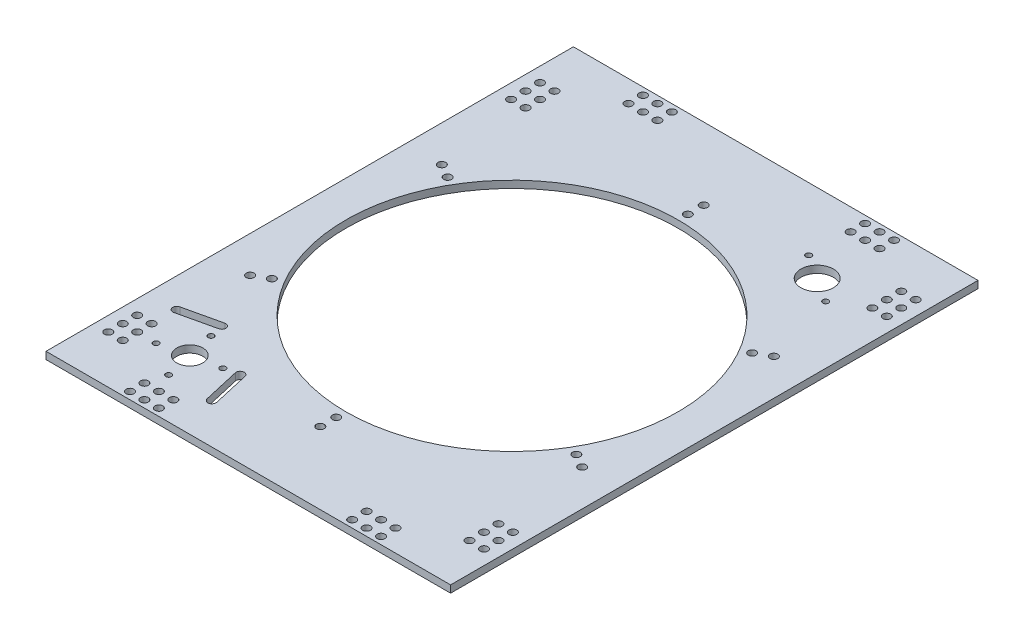
SolidWorks part; units mm, degrees
material "5052-H32"
ref_plane "Front Plane" through (0, 0, 0) normal (0, 0, 1) x (1, 0, 0)
ref_plane "Top Plane" through (0, 0, 0) normal (0, 1, 0) x (1, 0, 0)
ref_plane "Right Plane" through (0, 0, 0) normal (1, 0, 0) x (0, 0, -1)
sketch "Sketch1" plane through (0, 0, 0) normal (0, 1, 0) x (1, 0, 0)
  line L0 (-177.8, 231.775) -> (-177.8, -231.775)
  line L1 (-177.8, -231.775) -> (177.8, -231.775)
  line L2 (177.8, -231.775) -> (177.8, 231.775)
  line L3 (177.8, 231.775) -> (-177.8, 231.775)
  line L4 (0, 231.775) -> (0, -231.775) construction
  line L5 (-177.8, 0) -> (177.8, 0) construction
  line L6 (-127, 231.775) -> (-127, 206.375) construction
  line L7 (-127, 206.375) -> (-177.8, 206.375) construction
  line L8 (127, 206.375) -> (177.8, 206.375) construction
  line L9 (127, 231.775) -> (127, 206.375) construction
  line L10 (-127, -206.375) -> (-177.8, -206.375) construction
  line L11 (-127, -231.775) -> (-127, -206.375) construction
  line L12 (127, -231.775) -> (127, -206.375) construction
  line L13 (127, -206.375) -> (177.8, -206.375) construction
  line L14 (-127, -231.775) -> (-127, -203.2) construction
  line L15 (-127, -203.2) -> (-73.025, -203.2) construction
  line L16 (-73.025, -203.2) -> (-73.025, -231.775) construction
  line L17 (-177.8, -152.4) -> (-142.875, -152.4) construction
  line L18 (-142.875, -152.4) -> (-142.875, -206.375) construction
  line L19 (-116.9693, -147.6117) -> (-87.1462, -166.9791) construction
  line L29 (-102.1471, -157.2927) -> (0, 0) construction
  line L30 (-116.9693, -147.6117) -> (-105.9042, -195.8638) construction
  line L31 (-74.7675, -164.1404) -> (-67.387, -196.325) construction
  line L32 (-71.3015, -163.3456) -> (-63.9209, -195.5302)
  line L33 (-78.2336, -164.9352) -> (-70.853, -197.1198)
  line L34 (-87.1462, -166.9791) -> (-74.7675, -164.1404) construction
  line L35 (-118.3656, -141.4602) -> (-81.0867, -165.6694) construction
  line L36 (-81.0867, -165.6694) -> (-105.2959, -202.9483) construction
  line L37 (-105.2959, -202.9483) -> (-142.5748, -178.7391) construction
  line L38 (-142.5748, -178.7391) -> (-118.3656, -141.4602) construction
  line L39 (-116.9693, -147.6117) -> (-119.808, -135.233) construction
  line L40 (-119.808, -135.233) -> (-151.9926, -142.6136) construction
  line L41 (-102.1471, -157.2927) -> (-111.4368, -171.7378) construction
  line L42 (-119.0132, -138.6991) -> (-151.1978, -146.0796)
  line L43 (-120.6028, -131.767) -> (-152.7874, -139.1475)
  line L44 (0, 0) -> (105.6055, 162.6182) construction
  line L45 (84.3033, 176.4521) -> (126.9077, 148.7844) construction
  circle A0 centre (0, 0) radius 168.5 construction
  circle A1 centre (0, 0) radius 146.05
  circle A2 centre (0, 168.5) radius 3.429
  circle A3 centre (145.9253, 84.25) radius 3.429
  circle A4 centre (145.9253, -84.25) radius 3.429
  circle A5 centre (0, -168.5) radius 3.429
  circle A6 centre (-145.9253, -84.25) radius 3.429
  circle A7 centre (-145.9253, 84.25) radius 3.429
  circle A8 centre (-165.1, 189.7126) radius 3.429
  circle A9 centre (-152.4, 189.7126) radius 3.429
  circle A10 centre (-152.4, 177.0126) radius 3.429
  circle A11 centre (-165.1, 177.0126) radius 3.429
  circle A12 centre (-152.4, 164.3126) radius 3.429
  circle A13 centre (-165.1, 164.3126) radius 3.429
  circle A14 centre (165.1, 164.3126) radius 3.429
  circle A15 centre (152.4, 164.3126) radius 3.429
  circle A16 centre (165.1, 177.0126) radius 3.429
  circle A17 centre (152.4, 177.0126) radius 3.429
  circle A18 centre (152.4, 189.7126) radius 3.429
  circle A19 centre (165.1, 189.7126) radius 3.429
  circle A20 centre (165.1, -189.7126) radius 3.429
  circle A21 centre (152.4, -189.7126) radius 3.429
  circle A22 centre (152.4, -177.0126) radius 3.429
  circle A23 centre (165.1, -177.0126) radius 3.429
  circle A24 centre (152.4, -164.3126) radius 3.429
  circle A25 centre (165.1, -164.3126) radius 3.429
  circle A26 centre (-165.1, -164.3126) radius 3.429
  circle A27 centre (-152.4, -164.3126) radius 3.429
  circle A28 centre (-165.1, -177.0126) radius 3.429
  circle A29 centre (-152.4, -177.0126) radius 3.429
  circle A30 centre (-152.4, -189.7126) radius 3.429
  circle A31 centre (-165.1, -189.7126) radius 3.429
  circle A32 centre (-110.3376, 225.425) radius 3.429
  circle A33 centre (-97.6376, 225.425) radius 3.429
  circle A34 centre (-84.9376, 225.425) radius 3.429
  circle A35 centre (-97.6376, 212.725) radius 3.429
  circle A36 centre (-84.9376, 212.725) radius 3.429
  circle A37 centre (-110.3376, 212.725) radius 3.429
  circle A38 centre (110.3376, 212.725) radius 3.429
  circle A39 centre (84.9376, 212.725) radius 3.429
  circle A40 centre (97.6376, 212.725) radius 3.429
  circle A41 centre (84.9376, 225.425) radius 3.429
  circle A42 centre (97.6376, 225.425) radius 3.429
  circle A43 centre (110.3376, 225.425) radius 3.429
  circle A44 centre (110.3376, -225.425) radius 3.429
  circle A45 centre (97.6376, -225.425) radius 3.429
  circle A46 centre (84.9376, -225.425) radius 3.429
  circle A47 centre (97.6376, -212.725) radius 3.429
  circle A48 centre (84.9376, -212.725) radius 3.429
  circle A49 centre (110.3376, -212.725) radius 3.429
  circle A50 centre (-110.3376, -212.725) radius 3.429
  circle A51 centre (-84.9376, -212.725) radius 3.429
  circle A52 centre (-97.6376, -212.725) radius 3.429
  circle A53 centre (-84.9376, -225.425) radius 3.429
  circle A54 centre (-97.6376, -225.425) radius 3.429
  circle A55 centre (-110.3376, -225.425) radius 3.429
  arc A63 (-119.0132, -138.6991) -> (-120.6028, -131.767) centre (-119.808, -135.233) ccw
  arc A64 (-152.7874, -139.1475) -> (-151.1978, -146.0796) centre (-151.9926, -142.6136) ccw
  circle A69 centre (-116.9693, -147.6117) radius 2.54
  circle A70 centre (-87.1462, -166.9791) radius 2.54
  circle A71 centre (-105.9042, -195.8638) radius 2.54
  circle A72 centre (-135.5628, -177.2704) radius 2.54
  circle A73 centre (-111.4368, -171.7378) radius 11.43
  circle A74 centre (-111.4368, -171.7378) radius 21.0058 construction
  arc A75 (-71.3015, -163.3456) -> (-78.2336, -164.9352) centre (-74.7675, -164.1404) ccw
  arc A76 (-70.853, -197.1198) -> (-63.9209, -195.5302) centre (-67.387, -196.325) ccw
  circle A77 centre (-67.387, -196.325) radius 11.1125 construction
  circle A78 centre (-111.4368, -171.7378) radius 24.7523 construction
  circle A79 centre (105.6055, 162.6182) radius 14.2875
  circle A80 centre (84.3033, 176.4521) radius 2.54
  circle A81 centre (126.9077, 148.7844) radius 2.54
  circle A82 centre (0, 0) radius 154.5 construction
  circle A83 centre (0, 154.5) radius 3.429
  circle A84 centre (133.8009, 77.25) radius 3.429
  circle A85 centre (133.8009, -77.25) radius 3.429
  circle A86 centre (0, -154.5) radius 3.429
  circle A87 centre (-133.8009, -77.25) radius 3.429
  circle A88 centre (-133.8009, 77.25) radius 3.429
  point P8 (0, 0)
  point P28 (0, 0)
  point P143 (-99.7261, -153.5648)
  point P145 (91.7717, 141.316)
  point P148 (105.6055, 162.6182)
  point P165 (-91.7717, -141.316)
  point P171 (-71.0773, -180.2327)
  point P181 (-135.9003, -138.9233)
  point P200 (0, 0)
  dimension "D3" = 337
  dimension "D4" = 292.1
  dimension "D5" = 6.858
  dimension "D11" = 16.6624
  dimension "D13" = 6.858
  dimension "D18" = 16.6624
  dimension "D28" = 49.5046
  dimension "D34" = 35.56
  dimension "D32" = 4.3987
  dimension "D33" = 17.7037
  dimension "D37" = 5.08
  dimension "D38" = 17.1744
  dimension "D39" = 22.86
  dimension "D40" = 42.0116
  dimension "D49" = 22.225
  dimension "D43" = 28.575
  dimension "D51" = 5.08
  dimension "D52" = 309
  dimension "D53" = 6.858
  dimension "D1" = 355.6
  dimension "D2" = 463.55
  dimension "D7" = 60
  dimension "D8" = 60
  dimension "D9" = 25.4
  dimension "D10" = 50.8
  dimension "D12" = 12.7
  dimension "D15" = 12.7
  dimension "D17" = 12.7
  dimension "D19" = 6.35
  dimension "D22" = 12.7
  dimension "D23" = 12.7
  dimension "D24" = 9.525
  dimension "D25" = 53.975
  dimension "D26" = 9.525
  dimension "D27" = 53.975
  dimension "D30" = 44.45
  dimension "D31" = 44.45
  dimension "D29" = 19.0037
  dimension "D35" = 90
  dimension "D36" = 33
  dimension "D41" = 7.112
  dimension "D42" = 33.02
  dimension "D44" = 12.7
  dimension "D46" = 7.112
  dimension "D47" = 33.02
  dimension "D48" = 12.7
  dimension "D45" = 25.4
  dimension "D50" = 50.8
  dimension "D55" = 60
  dimension "D56" = 60
  dimension "D14" = 2
  dimension "D16" = 3
  dimension "D20" = 3
  dimension "D21" = 2
  dimension "D6" = 6
  dimension "D54" = 6
extrude "Boss-Extrude1" add sketch "Sketch1" along normal blind 6.35
